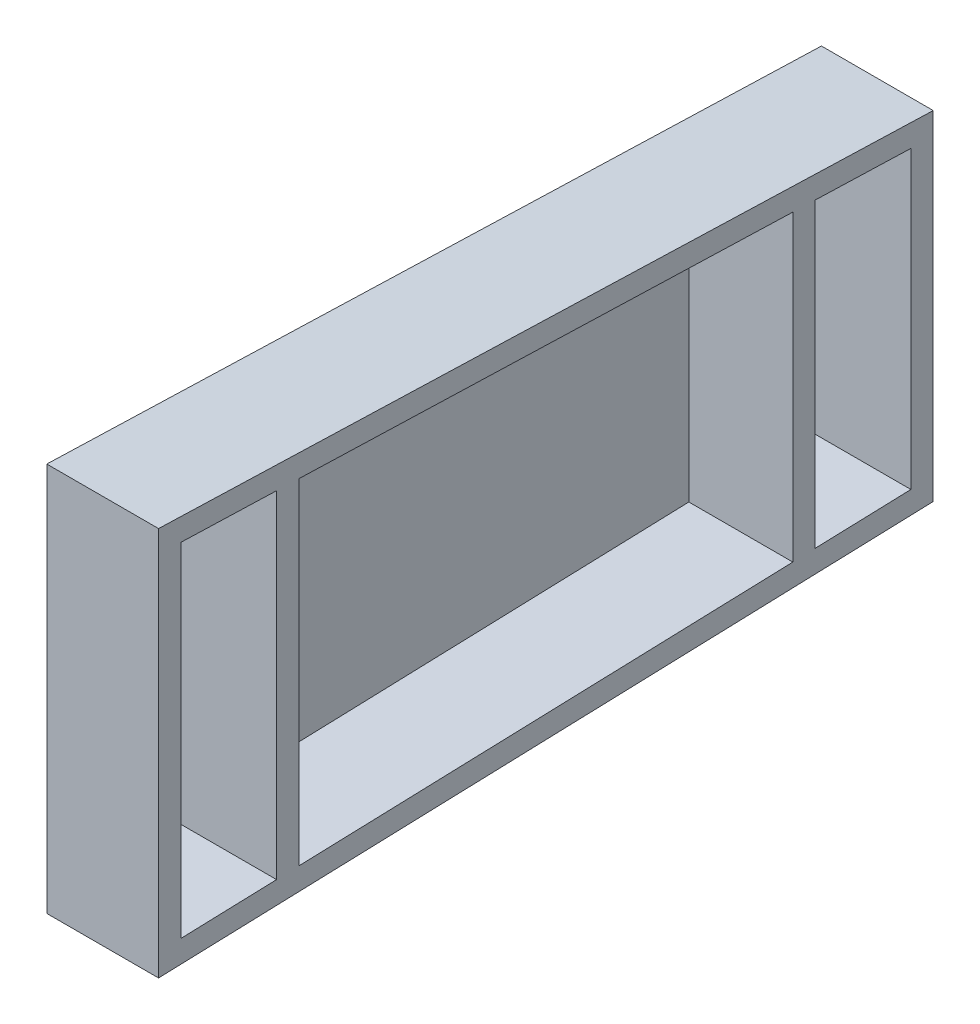
SolidWorks part; units mm, degrees
ref_plane "Front Plane" through (0, 0, 0) normal (0, 0, 1) x (1, 0, 0)
ref_plane "Top Plane" through (0, 0, 0) normal (0, 1, 0) x (1, 0, 0)
ref_plane "Right Plane" through (0, 0, 0) normal (1, 0, 0) x (0, 0, -1)
sketch "Sketch1" plane through (0, 0, 0) normal (1, 0, 0) x (0, 0, -1)
  line L0 (0, 74.865) -> (0, -74.865)
  line L1 (0, 74.865) -> (298, 65.13)
  line L2 (298, 65.13) -> (298, -65.13)
  line L3 (298, -65.13) -> (0, -74.865)
  point P0 (298, 0)
  point P4 (0, 0)
  dimension "D1" = 149.73
  dimension "D2" = 298
  dimension "D3" = 130.26
extrude "Boss-Extrude1" add sketch "Sketch1" along normal blind 3
sketch "Sketch2" plane through (3, 0, 0) normal (1, 0, 0) x (0, 0, -1)
  line L0 (0, 74.865) -> (298, 65.13)
  line L1 (298, 65.13) -> (298, 56.53)
  line L2 (298, -65.13) -> (298, 65.13) construction
  line L3 (289.4, 56.8109) -> (252.6, 58.0131)
  line L4 (0, 74.865) -> (0, -74.865) construction
  line L5 (0, 0) -> (298, 0) construction
  line L6 (0, 66.265) -> (0, 0)
  line L7 (0, 0) -> (8.6, 0)
  line L8 (8.6, 0) -> (8.6, 65.9841)
  line L9 (45.4, 0) -> (45.4, 64.7819)
  line L10 (54, 0) -> (54, 64.5009)
  line L11 (298, 0) -> (298, 56.53)
  line L12 (289.4, 56.8109) -> (289.4, 0)
  line L13 (244, 58.2941) -> (244, 0)
  line L14 (252.6, 58.0131) -> (252.6, 0)
  line L15 (8.6, 65.9841) -> (0, 66.265) construction
  line L16 (54, 64.5009) -> (45.4, 64.7819) construction
  line L17 (45.4, 64.7819) -> (8.6, 65.9841)
  line L18 (252.6, 58.0131) -> (244, 58.2941) construction
  line L19 (244, 58.2941) -> (54, 64.5009)
  line L20 (298, 56.53) -> (289.4, 56.8109) construction
  line L21 (45.4, 0) -> (54, 0)
  line L22 (244, 0) -> (252.6, 0)
  line L23 (289.4, 0) -> (298, 0)
  line L24 (0, 66.265) -> (0, 74.865)
  point P25 (149, 0)
  dimension "D1" = 8.6
  dimension "D3" = 95
  dimension "D4" = 95
  dimension "D6" = 8.6
  dimension "D2" = 8.6
  dimension "D5" = 8.6
  dimension "D7" = 8.6
  dimension "D8" = 8.6
extrude "Boss-Extrude2" add sketch "Sketch2" along normal blind 40
mirror "Mirror1" about plane through (43, 0, -45.4) normal (0, 1, 0) of "Boss-Extrude2"
equation "\"D2@Sketch2\"=\"D1@Sketch2\""
equation "\"D5@Sketch2\"=\"D6@Sketch2\""
equation "\"D7@Sketch2\"=\"D6@Sketch2\""
equation "\"D8@Sketch2\"=\"D6@Sketch2\""
